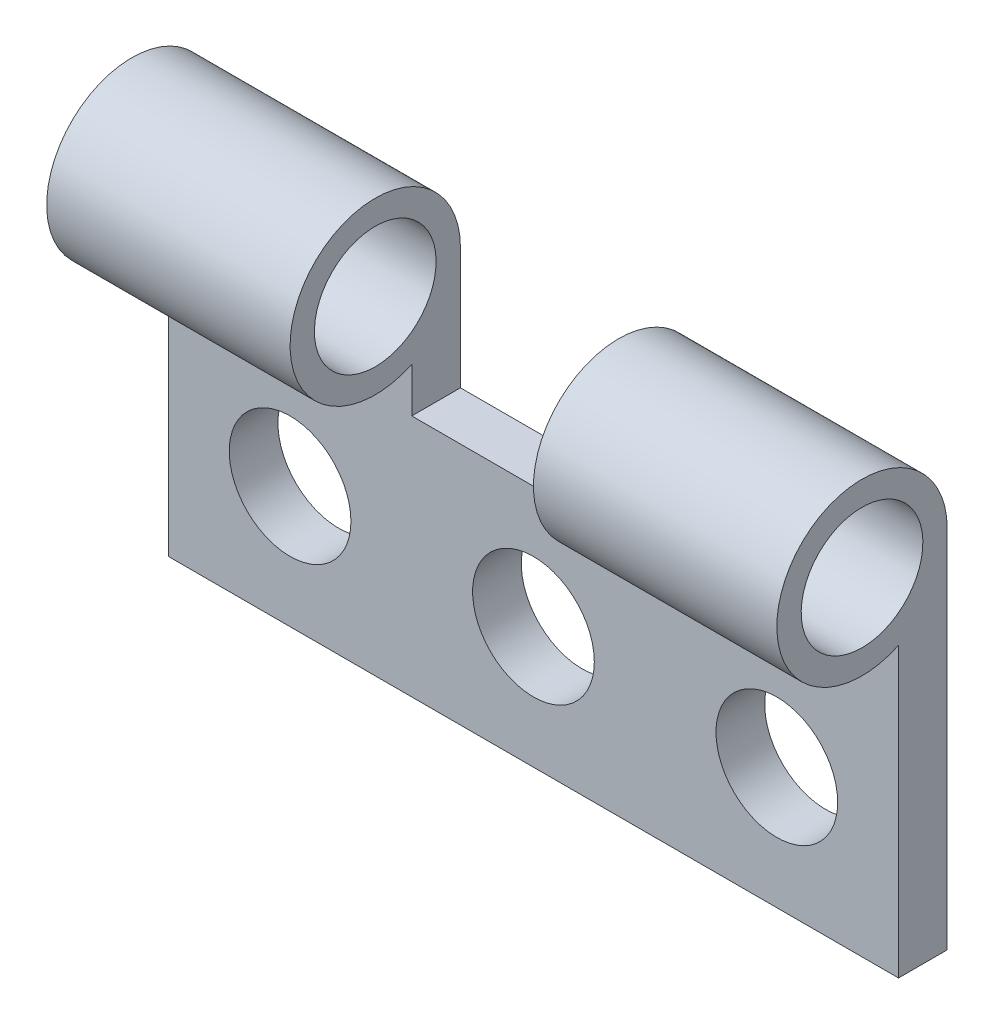
SolidWorks part; units mm, degrees
material "1060 Alloy"
ref_plane "Front Plane" through (0, 0, 0) normal (0, 0, 1) x (1, 0, 0)
ref_plane "Top Plane" through (0, 0, 0) normal (0, 1, 0) x (1, 0, 0)
ref_plane "Right Plane" through (0, 0, 0) normal (1, 0, 0) x (0, 0, -1)
sketch "Sketch1" plane through (0, 0, 0) normal (0, 0, 1) x (1, 0, 0)
  line L1 (-15, 5) -> (15, 5)
  line L2 (-15, 5) -> (-15, -5)
  line L3 (-15, -5) -> (15, -5)
  line L4 (15, 5) -> (15, -5)
  line L5 (-15, 5) -> (15, -5) construction
  line L6 (-15, -5) -> (15, 5) construction
  point P0 (0, 0)
  dimension "D1" = 30
  dimension "D2" = 10
extrude "Boss-Extrude1" add sketch "Sketch1" along normal blind 2
sketch "Sketch2" plane through (-15, 0, 0) normal (-1, 0, 0) x (0, 0, 1)
  line L1 (0, 5) -> (0, 10)
  line L2 (2, 5) -> (2, 6.8377)
  line L3 (0, 5) -> (2, 5)
  arc A0 (2, 6.8377) -> (0, 10) centre (3.5, 10) ccw
  circle A1 centre (3.5, 10) radius 2.5
  point P1 (3.4958, 9.8289)
  dimension "D1" = 7
  dimension "D2" = 5
  dimension "D3" = 5
extrude "Boss-Extrude2" add sketch "Sketch2" against normal blind 10
pattern_linear "LPattern1" count 2 spacing 20 along (1, 0, 0) of "Boss-Extrude2"
sketch "Sketch3" plane through (0, 0, 2) normal (0, 0, 1) x (1, 0, 0)
  line L0 (0, 5) -> (0, -5) construction
  line L1 (5, 5) -> (-5, 5) construction
  line L2 (-15, -5) -> (15, -5) construction
  line L3 (-15, 0) -> (15, 0) construction
  line L4 (-15, 6.8377) -> (-15, -5) construction
  line L5 (15, -5) -> (15, 6.8377) construction
  line L6 (-10, 0) -> (0, 0) construction
  circle A0 centre (-10, 0) radius 2.5
  circle A1 centre (0, 0) radius 2.5
  circle A2 centre (10, 0) radius 2.5
  dimension "D1" = 5
  dimension "D2" = 5
  dimension "D4" = 10
  dimension "D3" = 3
extrude "Cut-Extrude1" cut sketch "Sketch3" against normal blind 10
